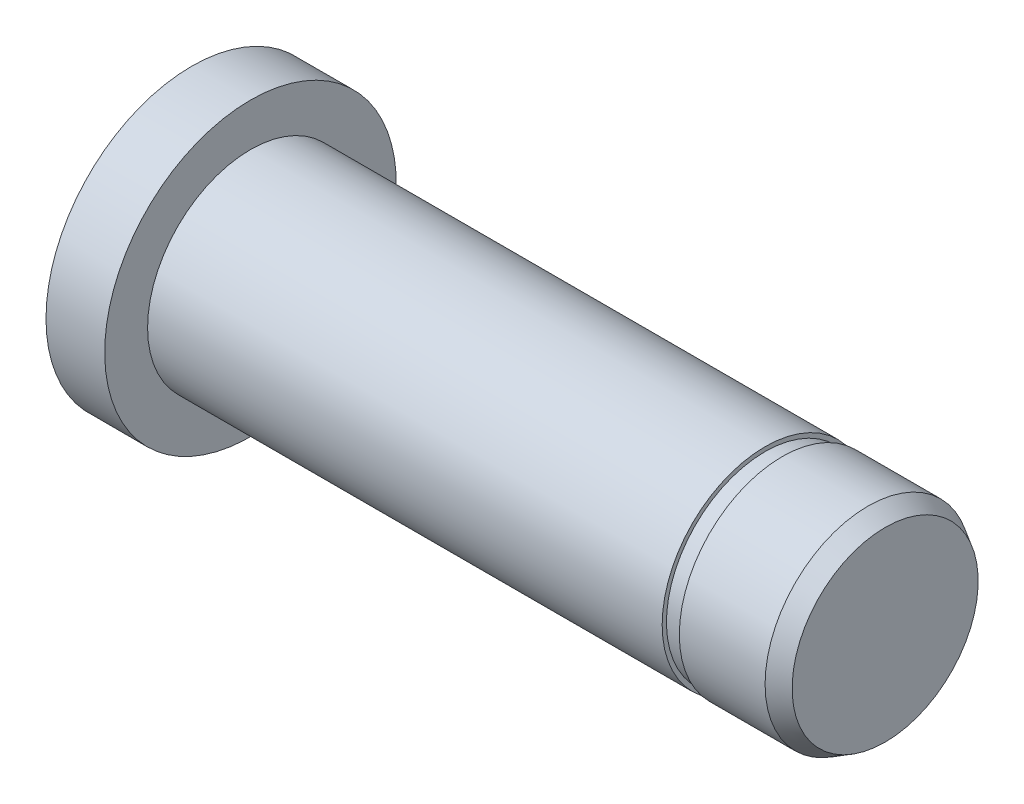
SolidWorks part; units mm, degrees
ref_plane "Płaszczyzna przednia" through (0, 0, 0) normal (0, 0, 1) x (1, 0, 0)
ref_plane "Płaszczyzna górna" through (0, 0, 0) normal (0, 1, 0) x (1, 0, 0)
ref_plane "Płaszczyzna prawa" through (0, 0, 0) normal (1, 0, 0) x (0, 0, -1)
sketch "Szkic1" plane through (0, 0, 0) normal (0, 0, 1) x (1, 0, 0)
  line L0 (0, 0) -> (0, 8.5)
  line L1 (0, 8.5) -> (4, 8.5)
  line L2 (4, 8.5) -> (4, 6)
  line L3 (4, 6) -> (41, 6)
  line L4 (41, 6) -> (41, 0)
  line L5 (41, 0) -> (0, 0)
  dimension "D1" = 4
  dimension "D2" = 8.5
  dimension "D3" = 6
  dimension "D4" = 37
revolve "Obrót1" add sketch "Szkic1" angle 360 about L5
chamfer "Sfazowanie1" distance 1 angle 30 2 edges at (41, 6, 0) (0, 8.5, 0)
sketch "Szkic2" plane through (41, 0, 0) normal (1, 0, 0) x (0, 0, -1)
  circle A0 centre (0, 0) radius 6
  circle A1 centre (0, 0) radius 5.75
  dimension "D1" = 12
  dimension "D2" = 11.5
extrude "Wytnij-wyciągnięcie1" cut sketch "Szkic2" against normal blind 1 from offset 6 offset against normal yes
